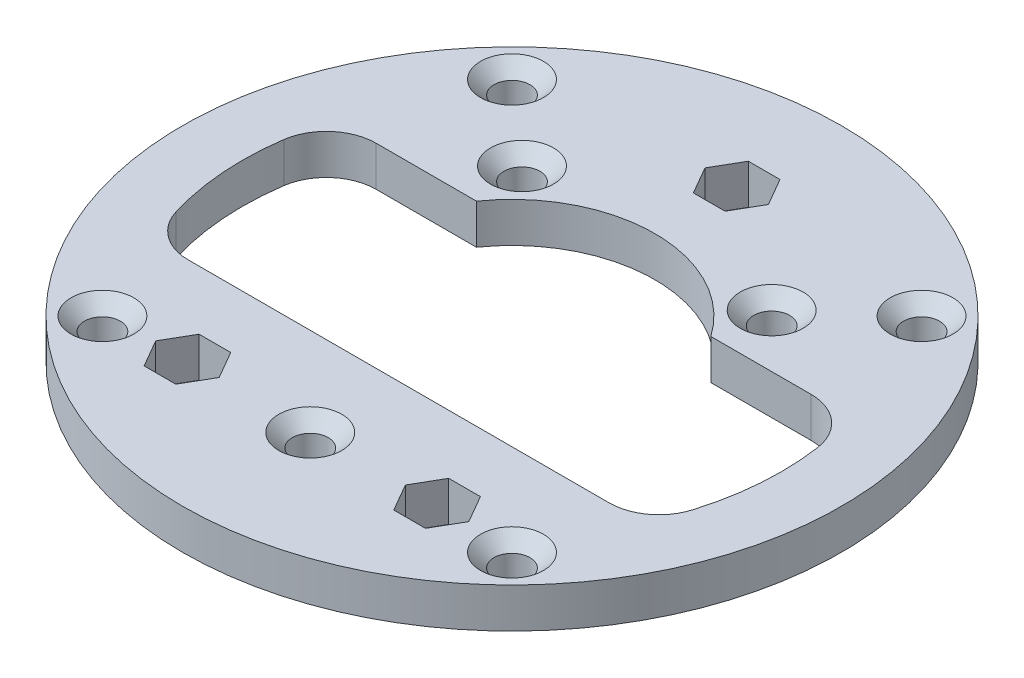
SolidWorks part; units mm, degrees
material "PEI"
ref_plane "Front Plane" through (0, 0, 0) normal (0, 0, 1) x (1, 0, 0)
ref_plane "Top Plane" through (0, 0, 0) normal (0, 1, 0) x (1, 0, 0)
ref_plane "Right Plane" through (0, 0, 0) normal (1, 0, 0) x (0, 0, -1)
sketch "Sketch1" plane through (0, 0, 0) normal (0, 1, 0) x (1, 0, 0)
  circle A0 centre (0, 0) radius 33
  circle A1 centre (0, 0) radius 27
  dimension "D1" = 66
  dimension "D2" = 6
extrude "Boss-Extrude1" add sketch "Sketch1" along normal blind 4
sketch "Sketch2" plane through (0, 4, 0) normal (0, 1, 0) x (1, 0, 0)
  line L0 (-24.5, -11.3468) -> (24.5, -11.3468)
  line L1 (-25.7325, 8.1755) -> (-11.7325, 8.1755)
  line L2 (0, 0) -> (7.7557, 0) construction
  line L3 (11.7325, 8.1755) -> (25.7325, 8.1755)
  line L4 (-20.5061, 20.5061) -> (0, 0) construction
  line L5 (-12.5, 13.5) -> (12.5, 13.5) construction
  circle A0 centre (0, 22.5) radius 2.25 construction
  circle A1 centre (-12.5, -20) radius 2.25 construction
  circle A2 centre (12.5, -20) radius 2.25 construction
  circle A4 centre (-12.5, 13.5) radius 1.5
  circle A6 centre (0, 0) radius 27 construction
  arc A8 (-11.7325, 8.1755) -> (11.7325, 8.1755) centre (0, 0) cw
  arc A9 (25.7325, 8.1755) -> (-25.7325, 8.1755) centre (0, 0) ccw
  arc A10 (24.5, -11.3468) -> (-24.5, -11.3468) centre (0, 0) cw
  circle A11 centre (12.5, 13.5) radius 1.5
  circle A12 centre (0, 0) radius 29 construction
  circle A13 centre (0, 0) radius 33 construction
  circle A14 centre (-20.5061, 20.5061) radius 1.75 construction
  circle A15 centre (20.5061, 20.5061) radius 1.75 construction
  circle A16 centre (20.5061, -20.5061) radius 1.75 construction
  circle A17 centre (-20.5061, -20.5061) radius 1.75 construction
  circle A18 centre (0, -20.2) radius 1.5
  point P15 (0, 13.5)
  point P19 (0, 0)
  point P44 (0, 0)
  circle M2 centre (0, 0) radius 27
  dimension "D5" = 4.5
  dimension "D6" = 4.5
  dimension "D7" = 4.5
  dimension "D12" = 14.3
  dimension "D16" = 3.5
  dimension "D11" = 3
  dimension "D1" = 25
  dimension "D2" = 12.5
  dimension "D3" = 22.5
  dimension "D4" = 20
  dimension "D14" = 4
  dimension "D15" = 135
  dimension "D8" = 14
  dimension "D9" = 14
  dimension "D10" = 49
  dimension "D18" = 25
  dimension "D19" = 20.2
  dimension "D13" = 13.5
  dimension "D17" = 4
extrude "Saliente-Extruir1" add sketch "Sketch2" against normal up to surface (4 mm away) contours L1 A8 L3 M2 | L0 M2 up to face at (0, 0, 33)
sketch "Croquis1" plane through (0, 4, 0) normal (0, 1, 0) x (1, 0, 0)
  line L1 (-9.3246, -20) -> (-10.9123, -17.25)
  line L2 (-10.9123, -17.25) -> (-14.0877, -17.25)
  line L3 (-14.0877, -17.25) -> (-15.6754, -20)
  line L4 (-15.6754, -20) -> (-14.0877, -22.75)
  line L5 (-14.0877, -22.75) -> (-10.9123, -22.75)
  line L6 (-10.9123, -22.75) -> (-9.3246, -20)
  line L7 (15.6754, -20) -> (14.0877, -17.25)
  line L8 (14.0877, -17.25) -> (10.9123, -17.25)
  line L9 (10.9123, -17.25) -> (9.3246, -20)
  line L10 (9.3246, -20) -> (10.9123, -22.75)
  line L11 (10.9123, -22.75) -> (14.0877, -22.75)
  line L12 (14.0877, -22.75) -> (15.6754, -20)
  line L13 (3.1754, 22.5) -> (1.5877, 25.25)
  line L14 (1.5877, 25.25) -> (-1.5877, 25.25)
  line L15 (-1.5877, 25.25) -> (-3.1754, 22.5)
  line L16 (-3.1754, 22.5) -> (-1.5877, 19.75)
  line L17 (-1.5877, 19.75) -> (1.5877, 19.75)
  line L18 (1.5877, 19.75) -> (3.1754, 22.5)
  circle A0 centre (-20.5061, 20.5061) radius 1.75 construction
  circle A1 centre (-20.5061, 20.5061) radius 1.75
  circle A4 centre (20.5061, 20.5061) radius 1.75 construction
  circle A5 centre (20.5061, 20.5061) radius 1.75
  circle A6 centre (-12.5, -20) radius 2.75 construction
  circle A7 centre (12.5, -20) radius 2.75 construction
  circle A8 centre (0, 22.5) radius 2.75 construction
  circle A16 centre (-20.5061, -20.5061) radius 1.75 construction
  circle A17 centre (-20.5061, -20.5061) radius 1.75
  circle A18 centre (20.5061, -20.5061) radius 1.75 construction
  circle A19 centre (20.5061, -20.5061) radius 1.75
  dimension "D1" = 5.5
  dimension "D2" = 5.5
  dimension "D3" = 5.5
extrude "Cortar-Extruir1" cut sketch "Croquis1" against normal up to next
hole_wizard "CSK for M3 Flat Head Machine Screw1" positions "Sketch4" profile "Sketch5" countersink size "M3" standard "ANSI Metric" end condition through all
sketch "Sketch4" plane through (0, 4, 0) normal (0, 1, 0) x (1, 0, 0)
  point P0 (-20.5061, 20.5061)
  point P3 (20.5061, 20.5061)
  point P6 (20.5061, -20.5061)
  point P9 (-20.5061, -20.5061)
sketch "Sketch5" plane through (-20.5061, 4, -20.5061) normal (1, 0, 0) x (0, 0, 1)
  line L0 (0, 0) -> (0, 4)
  line L1 (0, 4) -> (1.8, 4)
  line L2 (1.8, 4) -> (1.8, 1.35)
  line L3 (1.8, 1.35) -> (3.15, 0)
  line L5 (3.15, 0) -> (0, 0)
  line L6 (-1.8, 1.35) -> (-3.15, 0) construction
  line L11 (0, -6.35) -> (0, 107.95) construction
  dimension "Thru Hole Dia." = 3.6
  dimension "Thru Hole Depth" = 4
  dimension "Near C'Sink Dia." = 6.3
  dimension "Near C'Sink Angle" = 90
hole_wizard "CSK for M3 Flat Head Machine Screw2" positions "Sketch6" profile "Sketch7" countersink size "M3" standard "ANSI Metric" end condition through all
sketch "Sketch6" plane through (0, 4, 0) normal (0, 1, 0) x (1, 0, 0)
  point P12 (-12.5, 13.5)
  point P15 (12.5, 13.5)
  point P18 (0, -20.2)
sketch "Sketch7" plane through (-12.5, 4, -13.5) normal (1, 0, 0) x (0, 0, 1)
  line L0 (0, 0) -> (0, 4)
  line L1 (0, 4) -> (1.8, 4)
  line L2 (1.8, 4) -> (1.8, 1.35)
  line L3 (1.8, 1.35) -> (3.15, 0)
  line L5 (3.15, 0) -> (0, 0)
  line L6 (-1.8, 1.35) -> (-3.15, 0) construction
  line L11 (0, -6.35) -> (0, 107.95) construction
  dimension "Thru Hole Dia." = 3.6
  dimension "Thru Hole Depth" = 4
  dimension "Near C'Sink Dia." = 6.3
  dimension "Near C'Sink Angle" = 90
fillet "Fillet1" radius 5 4 edges at (-25.7325, 2, -8.1755) (25.7325, 2, -8.1755) (24.5, 2, 11.3468) (-24.5, 2, 11.3468)
equation "\"D2@Sketch2\"=\"D1@Sketch2\"/2"
equation "\"D6@Sketch2\"=\"D5@Sketch2\""
equation "\"D7@Sketch2\"=\"D6@Sketch2\""
equation "\"D2@Croquis1\"=\"D3@Croquis1\""
equation "\"D1@Croquis1\"=\"D3@Croquis1\""
